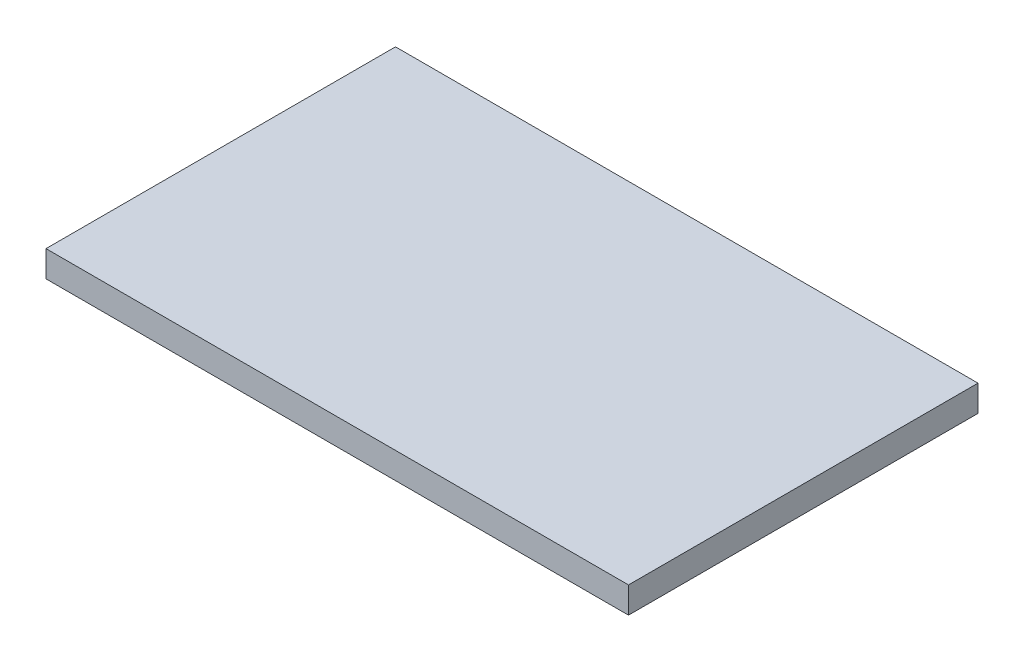
SolidWorks part; units mm, degrees
ref_plane "Front" through (0, 0, 0) normal (0, 0, 1) x (1, 0, 0)
ref_plane "Top" through (0, 0, 0) normal (0, 1, 0) x (1, 0, 0)
ref_plane "Right" through (0, 0, 0) normal (1, 0, 0) x (0, 0, -1)
sketch "Sketch1" plane through (0, 0, 0) normal (0, 1, 0) x (1, 0, 0)
  line L1 (0, 0) -> (10, 0)
  line L2 (0, 0) -> (0, 6)
  line L3 (0, 6) -> (10, 6)
  line L4 (10, 0) -> (10, 6)
  dimension "D1" = 10
  dimension "D2" = 6
extrude "Boss-Extrude1" add sketch "Sketch1" along normal blind 0.45
